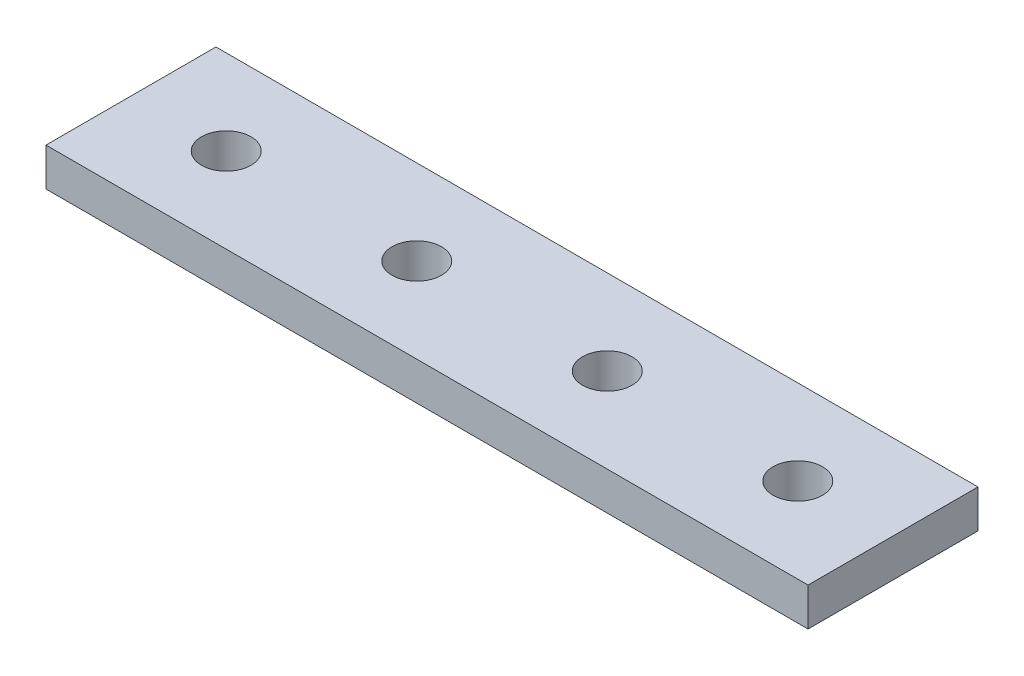
SolidWorks part; units mm, degrees
ref_plane "Front Plane" through (0, 0, 0) normal (0, 0, 1) x (1, 0, 0)
ref_plane "Top Plane" through (0, 0, 0) normal (0, 1, 0) x (1, 0, 0)
ref_plane "Right Plane" through (0, 0, 0) normal (1, 0, 0) x (0, 0, -1)
sketch "Sketch1" plane through (0, 0, 0) normal (0, 1, 0) x (1, 0, 0)
  line L0 (-50, 0) -> (-37.5, 0) construction
  line L1 (-50, -11.15) -> (50, -11.15)
  line L2 (-50, -11.15) -> (-50, 11.15)
  line L3 (-50, 11.15) -> (50, 11.15)
  line L4 (50, -11.15) -> (50, 11.15)
  line L5 (-50, -11.15) -> (50, 11.15) construction
  line L6 (-50, 11.15) -> (50, -11.15) construction
  circle A0 centre (-37.5, 0) radius 3.25
  circle A1 centre (-12.5, 0) radius 3.25
  circle A2 centre (12.5, 0) radius 3.25
  circle A3 centre (37.5, 0) radius 3.25
  point P0 (0, 0)
  point P10 (0, 0)
  point P16 (-12.5, 0)
  dimension "D4" = 6.5
  dimension "D1" = 100
  dimension "D2" = 22.3
  dimension "D3" = 12.5
  dimension "D6" = 25
  dimension "D5" = 4
extrude "Boss-Extrude1" add sketch "Sketch1" against normal blind 5
